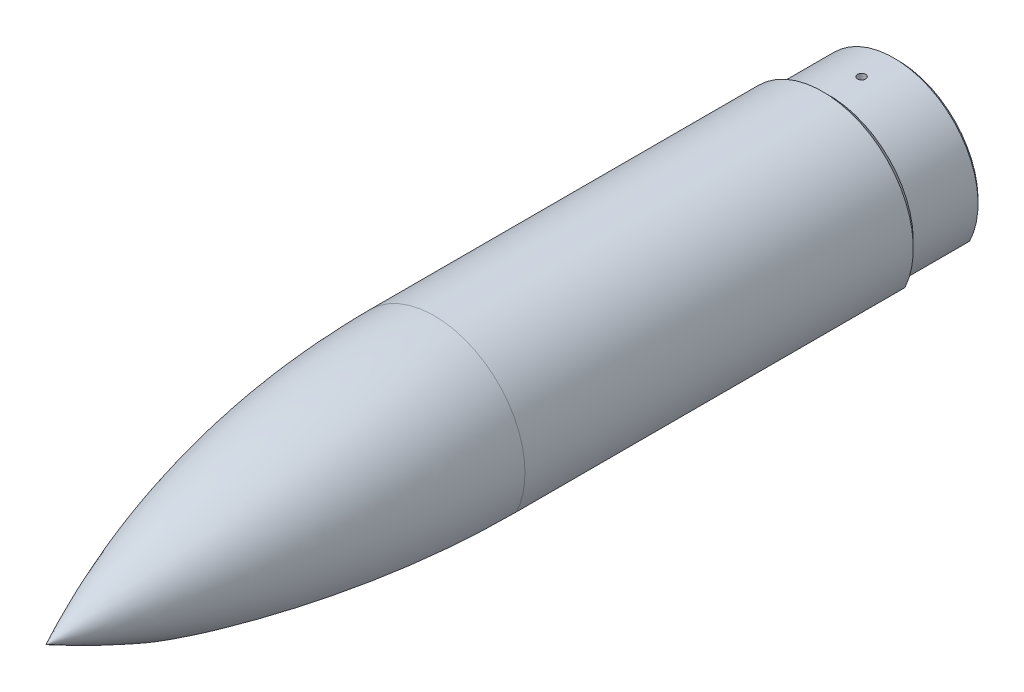
SolidWorks part; units mm, degrees
ref_plane "Front Plane" through (0, 0, 0) normal (0, 0, 1) x (1, 0, 0)
ref_plane "Top Plane" through (0, 0, 0) normal (0, 1, 0) x (1, 0, 0)
ref_plane "Right Plane" through (0, 0, 0) normal (1, 0, 0) x (0, 0, -1)
sketch "Sketch1" plane through (0, 0, 0) normal (1, 0, 0) x (0, 0, -1)
  line L0 (0, 0) -> (110.0352, 0) construction
  line L1 (152.4, 17.78) -> (76.2, 17.78)
  line L2 (153.67, 15.24) -> (76.2, 15.24)
  line L5 (5.9274, 0) -> (0, 0)
  line L9 (167.04, 15.24) -> (153.67, 15.24)
  line L10 (153.67, 16.51) -> (166.37, 16.51)
  line L11 (152.4, 17.78) -> (153.67, 16.51)
  line L12 (166.37, 16.51) -> (167.04, 15.84)
  line L13 (167.04, 15.84) -> (167.04, 15.24)
  arc A0 (76.2, 17.78) -> (0, 0) centre (76.2, -154.3957) ccw
  arc A1 (76.2, 15.24) -> (5.9274, 0) centre (76.2, -154.3957) ccw
  point P10 (151.6074, 16.51)
  point P12 (150.3289, 17.78)
  point P13 (151.599, 16.51)
  point P15 (150.2665, 17.78)
  point P16 (150.2932, 17.78)
  point P17 (167.04, 15.84)
  point P18 (153.67, 15.24)
  point P20 (0, 0)
  dimension "D1" = 2.54
  dimension "D2" = 12.7
  dimension "D3" = 76.2
  dimension "D4" = 15.24
  dimension "D5" = 1.27
  dimension "D6" = 0.6
  dimension "D7" = 1.27
  dimension "D8" = 135
  dimension "D9" = 76.2
revolve "Revolve1" add sketch "Sketch1" angle 360 about L0
sketch "Sketch2" plane through (0, 0, -167.04) normal (0, 0, -1) x (-1, 0, 0)
  line L0 (15.4419, -5.842) -> (-15.4419, -5.842) construction
  line L1 (-16.1764, -3.302) -> (16.1764, -3.302) construction
  line L2 (0, 0) -> (0, -86.36) construction
  circle A0 centre (0, 0) radius 16.51 construction
  circle A1 centre (0, 0) radius 16.51 construction
  circle A2 centre (0, -86.36) radius 80.518
  dimension "D3" = 161.036
  dimension "D1" = 2.54
  dimension "D2" = 3.302
extrude "Cut-Extrude1" cut sketch "Sketch2" against normal up to vertex
sketch "Sketch3" plane through (0, 0, 0) normal (0, 1, 0) x (1, 0, 0)
  line L0 (16.51, 153.67) -> (-16.51, 153.67) construction
  circle A0 centre (0, 160.02) radius 0.8001
  point P4 (0, 160.02)
  dimension "D1" = 6.35
  dimension "D2" = 1.6002
extrude "Cut-Extrude2" cut sketch "Sketch3" along normal up to surface (16.51 mm away)
